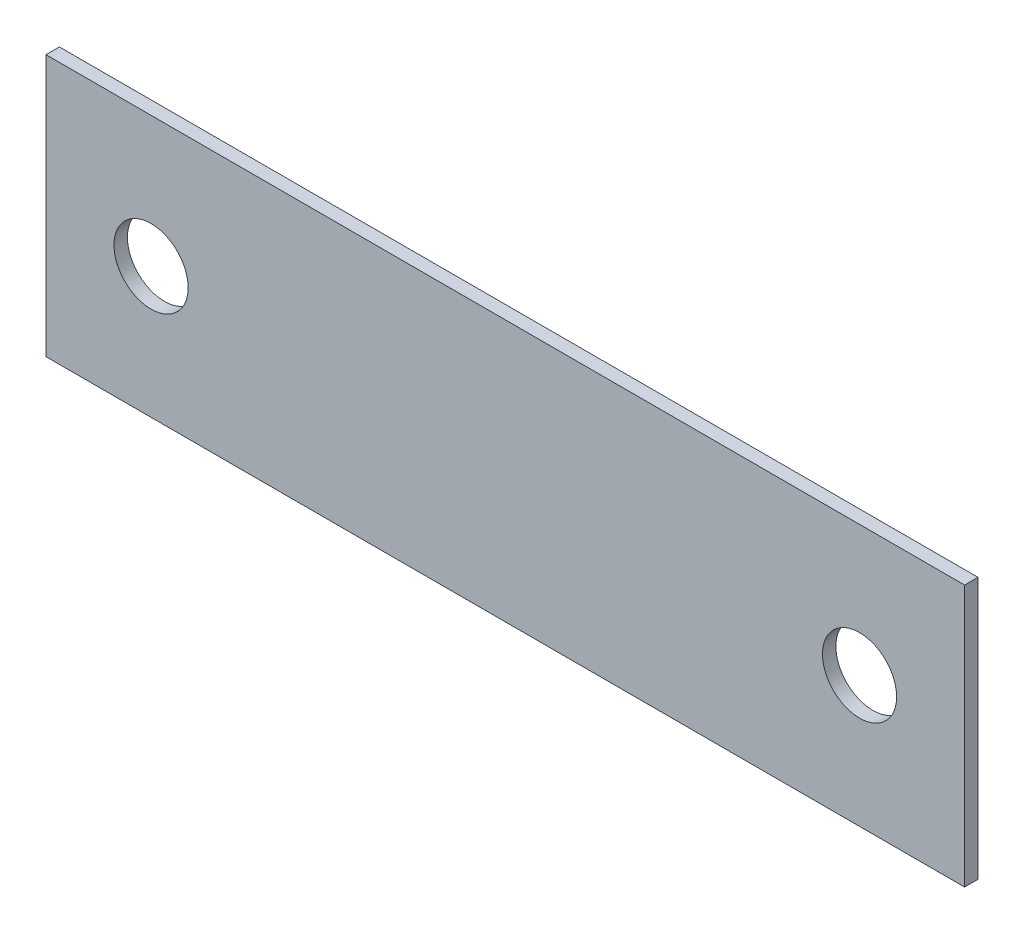
SolidWorks part; units mm, degrees
ref_plane "Front Plane" through (0, 0, 0) normal (0, 0, 1) x (1, 0, 0)
ref_plane "Top Plane" through (0, 0, 0) normal (0, 1, 0) x (1, 0, 0)
ref_plane "Right Plane" through (0, 0, 0) normal (1, 0, 0) x (0, 0, -1)
sketch "Sketch2" plane through (0, 0, 0) normal (0, 0, 1) x (1, 0, 0)
  line L1 (-30.5785, 16.9368) -> (25.1745, 16.9368)
  line L2 (-30.5785, 16.9368) -> (-30.5785, 1.0618)
  line L3 (-30.5785, 1.0618) -> (25.1745, 1.0618)
  line L4 (25.1745, 16.9368) -> (25.1745, 1.0618)
  dimension "D1" = 55.753
  dimension "D2" = 15.875
extrude "Boss-Extrude1" add sketch "Sketch2" along normal blind 0.8128
hole_wizard "M4 Clearance Hole1" positions "Sketch4" profile "Sketch3" hole size "M4" standard "ANSI Metric" end condition through all
sketch "Sketch4" plane through (0, 0, 0.8128) normal (0, 0, 1) x (1, 0, 0)
  line L0 (-30.5785, 16.9368) -> (-30.5785, 1.0618) construction
  line L1 (25.1745, 16.9368) -> (-30.5785, 16.9368) construction
  point P0 (-24.2018, 8.9993)
  point P2 (18.7979, 8.9993)
  dimension "D1" = 42.9997
  dimension "D2" = 6.3767
  dimension "D3" = 7.9375
  dimension "D4" = 7.9375
sketch "Sketch3" plane through (-24.2018, 8.9993, 0.8128) normal (1, 0, 0) x (0, -1, 0)
  line L0 (0, 0) -> (0, 0.8128)
  line L1 (0, 0.8128) -> (2.25, 0.8128)
  line L2 (2.25, 0.8128) -> (2.25, 0)
  line L5 (2.25, 0) -> (0, 0)
  line L11 (0, -6.35) -> (0, 107.95) construction
  dimension "Thru Hole Dia." = 4.5
  dimension "Thru Hole Depth" = 0.8128
